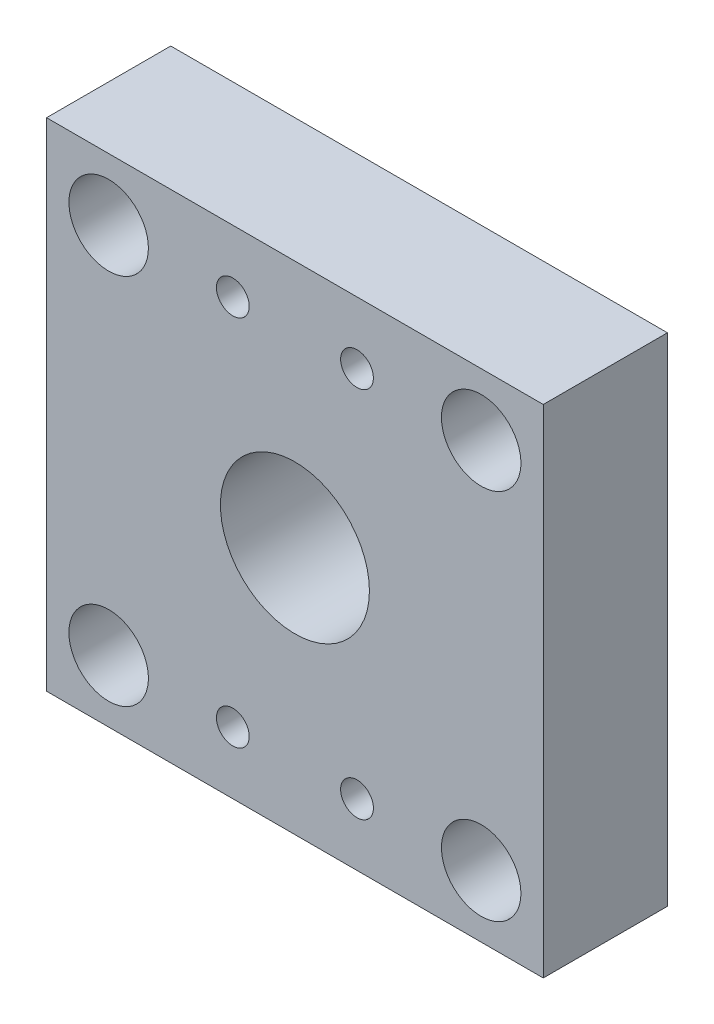
SolidWorks part; units mm, degrees
material "1023 Carbon Steel Sheet (SS)"
ref_plane "Front Plane" through (0, 0, 0) normal (0, 0, 1) x (1, 0, 0)
ref_plane "Top Plane" through (0, 0, 0) normal (0, 1, 0) x (1, 0, 0)
ref_plane "Right Plane" through (0, 0, 0) normal (1, 0, 0) x (0, 0, -1)
sketch "Sketch1" plane through (0, 0, 0) normal (0, 0, 1) x (1, 0, 0)
  line L1 (0, 0) -> (50.8, 0)
  line L2 (0, 0) -> (0, 50.8)
  line L3 (0, 50.8) -> (50.8, 50.8)
  line L4 (50.8, 0) -> (50.8, 50.8)
  dimension "D1" = 50.8
  dimension "D2" = 50.8
extrude "Boss-Extrude1" add sketch "Sketch1" along normal blind 12.7
sketch "Sketch2" plane through (0, 0, 12.7) normal (0, 0, 1) x (1, 0, 0)
  line L0 (0, 25.4) -> (50.8, 25.4) construction
  line L1 (0, 50.8) -> (0, 0) construction
  line L2 (50.8, 0) -> (50.8, 50.8) construction
  line L3 (50.8, 25.4) -> (25.4, 50.8) construction
  line L4 (50.8, 50.8) -> (0, 50.8) construction
  line L5 (25.4, 50.8) -> (25.4, 0) construction
  line L6 (0, 0) -> (50.8, 0) construction
  circle A0 centre (25.4, 25.4) radius 7.62
  dimension "D1" = 15.24
extrude "Cut-Extrude1" cut sketch "Sketch2" against normal through all
sketch "Sketch3" plane through (0, 0, 12.7) normal (0, 0, 1) x (1, 0, 0)
  line L0 (0, 25.4) -> (50.8, 25.4) construction
  line L1 (0, 50.8) -> (0, 0) construction
  line L2 (50.8, 0) -> (50.8, 50.8) construction
  line L3 (50.8, 25.4) -> (25.4, 0) construction
  line L4 (0, 0) -> (50.8, 0) construction
  line L5 (25.4, 0) -> (25.4, 50.8) construction
  line L6 (50.8, 50.8) -> (0, 50.8) construction
  circle A0 centre (6.35, 44.45) radius 4.064
  circle A1 centre (6.35, 6.35) radius 4.064
  circle A2 centre (44.45, 44.45) radius 4.064
  circle A3 centre (44.45, 6.35) radius 4.064
  dimension "D3" = 8.128
  dimension "D1" = 6.35
  dimension "D2" = 6.35
extrude "Cut-Extrude2" cut sketch "Sketch3" against normal through all
sketch "Sketch4" plane through (0, 0, 12.7) normal (0, 0, 1) x (1, 0, 0)
  line L0 (0, 25.4) -> (50.8, 25.4) construction
  line L1 (0, 50.8) -> (0, 0) construction
  line L2 (50.8, 0) -> (50.8, 50.8) construction
  line L3 (50.8, 25.4) -> (25.4, 0) construction
  line L4 (0, 0) -> (50.8, 0) construction
  line L5 (25.4, 0) -> (25.4, 50.8) construction
  line L6 (50.8, 50.8) -> (0, 50.8) construction
  circle A0 centre (19.05, 44.45) radius 1.6764
  circle A1 centre (31.75, 44.45) radius 1.6764
  circle A2 centre (19.05, 6.35) radius 1.6764
  circle A3 centre (31.75, 6.35) radius 1.6764
  dimension "D1" = 3.3528
  dimension "D2" = 6.35
  dimension "D3" = 6.35
extrude "Cut-Extrude3" cut sketch "Sketch4" against normal through all
